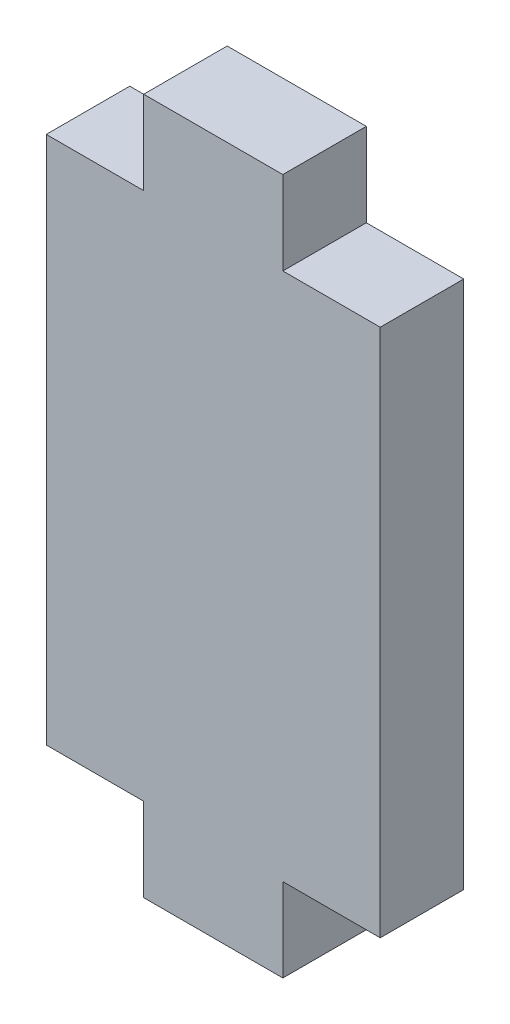
SolidWorks part; units mm, degrees
ref_plane "Alzado" through (0, 0, 0) normal (0, 0, 1) x (1, 0, 0)
ref_plane "Planta" through (0, 0, 0) normal (0, 1, 0) x (1, 0, 0)
ref_plane "Vista lateral" through (0, 0, 0) normal (1, 0, 0) x (0, 0, -1)
sketch "Croquis1" plane through (0, 0, 0) normal (0, 0, 1) x (1, 0, 0)
  line L0 (-6, 9.5) -> (-2.5, 9.5)
  line L2 (-6, 9.5) -> (-6, -9.5)
  line L4 (6, 9.5) -> (6, -9.5)
  line L5 (-6, 9.5) -> (6, -9.5) construction
  line L6 (-6, -9.5) -> (6, 9.5) construction
  line L7 (-2.5, 9.5) -> (-2.5, 12.5)
  line L8 (-2.5, 12.5) -> (2.5, 12.5)
  line L9 (2.5, 12.5) -> (2.5, 9.5)
  line L10 (2.5, 9.5) -> (6, 9.5)
  line L11 (6, -9.5) -> (2.5, -9.5)
  line L12 (2.5, -9.5) -> (2.5, -12.5)
  line L13 (2.5, -12.5) -> (-2.5, -12.5)
  line L14 (-2.5, -12.5) -> (-2.5, -9.5)
  line L15 (-2.5, -9.5) -> (-6, -9.5)
  point P0 (0, 0)
  dimension "D1" = 5
  dimension "D2" = 3
  dimension "D3" = 12
  dimension "D4" = 19
extrude "Saliente-Extruir1" add sketch "Croquis1" along normal blind 3
